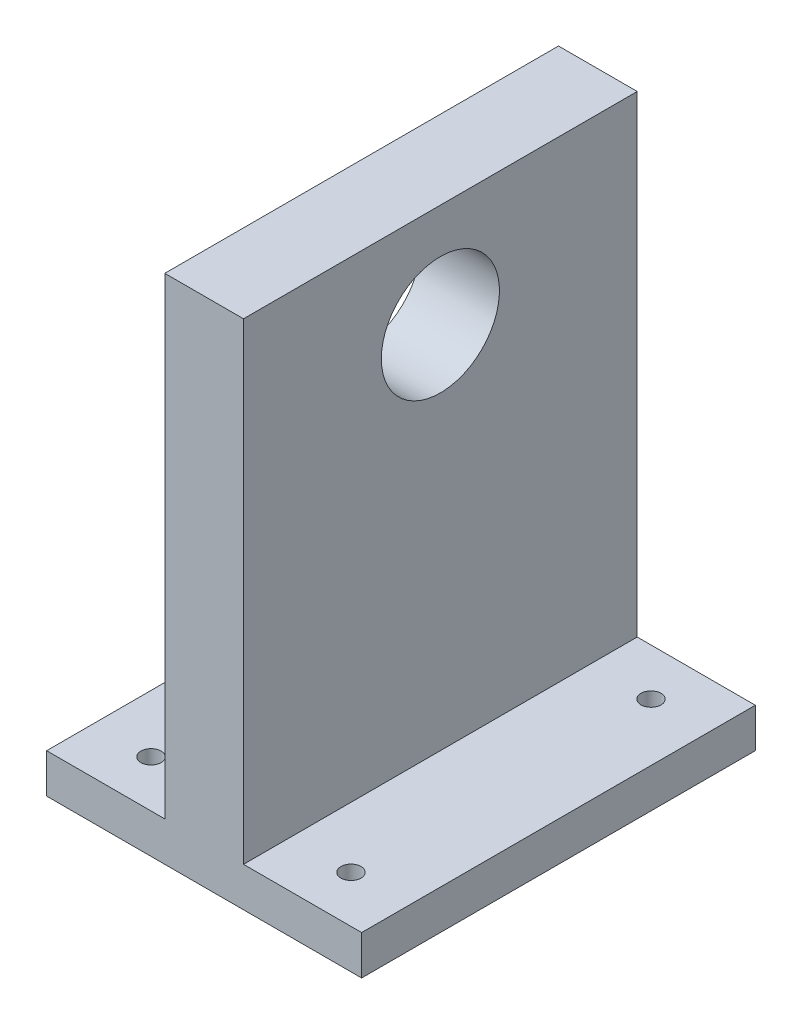
SolidWorks part; units mm, degrees
ref_plane "Front Plane" through (0, 0, 0) normal (0, 0, 1) x (1, 0, 0)
ref_plane "Top Plane" through (0, 0, 0) normal (0, 1, 0) x (1, 0, 0)
ref_plane "Right Plane" through (0, 0, 0) normal (1, 0, 0) x (0, 0, -1)
sketch "Sketch2" plane through (0, 0, 0) normal (0, 1, 0) x (1, 0, 0)
  line L1 (-40, -50) -> (40, -50)
  line L2 (-40, -50) -> (-40, 50)
  line L3 (-40, 50) -> (40, 50)
  line L4 (40, -50) -> (40, 50)
  line L5 (-40, -50) -> (40, 50) construction
  line L6 (-40, 50) -> (40, -50) construction
  point P0 (0, 0)
  dimension "D1" = 100
  dimension "D2" = 80
extrude "Boss-Extrude1" add sketch "Sketch2" along normal blind 10 contours L2 L3 L4 L1
sketch "Sketch3" plane through (0, 10, 0) normal (0, 1, 0) x (1, 0, 0)
  line L0 (-40, 50) -> (40, 50) construction
  line L1 (-10, -50) -> (10, -50)
  line L2 (-10, -50) -> (-10, 50)
  line L3 (-10, 50) -> (10, 50)
  line L4 (10, -50) -> (10, 50)
  line L5 (-10, -50) -> (10, 50) construction
  line L6 (-10, 50) -> (10, -50) construction
  point P0 (0, 0)
  dimension "D1" = 20
extrude "Boss-Extrude2" add sketch "Sketch3" along normal blind 120
sketch "Sketch4" plane through (-10, 0, 0) normal (-1, 0, 0) x (0, 0, 1)
  line L0 (0, 130) -> (0, 0) construction
  line L1 (-50, 130) -> (50, 130) construction
  line L6 (50, 0) -> (-50, 0) construction
  circle A1 centre (0, 103.69) radius 0.75
  circle A2 centre (0, 103.69) radius 15
  dimension "D7" = 1.5
  dimension "D2" = 30
  dimension "D1" = 103.69
sketch "Sketch5" plane through (0, 0, 0) normal (0, -1, 0) x (1, 0, 0)
  line L0 (0, 50) -> (0, -50) construction
  line L1 (-40, 50) -> (40, 50) construction
  line L2 (-40, -50) -> (40, -50) construction
  line L3 (-40, 0) -> (40, 0) construction
  line L4 (-40, 50) -> (-40, -50) construction
  line L5 (40, 50) -> (40, -50) construction
  line L6 (-40, 38.1) -> (40, 38.1) construction
  line L7 (-40, -38.1) -> (40, -38.1) construction
  line L8 (-25.4, 50) -> (-25.4, -50) construction
  line L9 (25.4, 50) -> (25.4, -50) construction
  circle A0 centre (-25.4, -38.1) radius 2.555
  circle A1 centre (25.4, -38.1) radius 2.555
  circle A2 centre (-25.4, 38.1) radius 2.555
  circle A3 centre (25.4, 38.1) radius 2.555
  dimension "D5" = 5.11
  dimension "D1" = 76.2
  dimension "D2" = 38.1
  dimension "D3" = 50.8
  dimension "D4" = 25.4
extrude "Cut-Extrude2" cut sketch "Sketch5" against normal blind 55 contours A2 | A0 | A1 | A3
fillet "Fillet2" [suppressed] radius 20
extrude "Cut-Extrude3" cut sketch "Sketch4" against normal blind 29 contours A2
